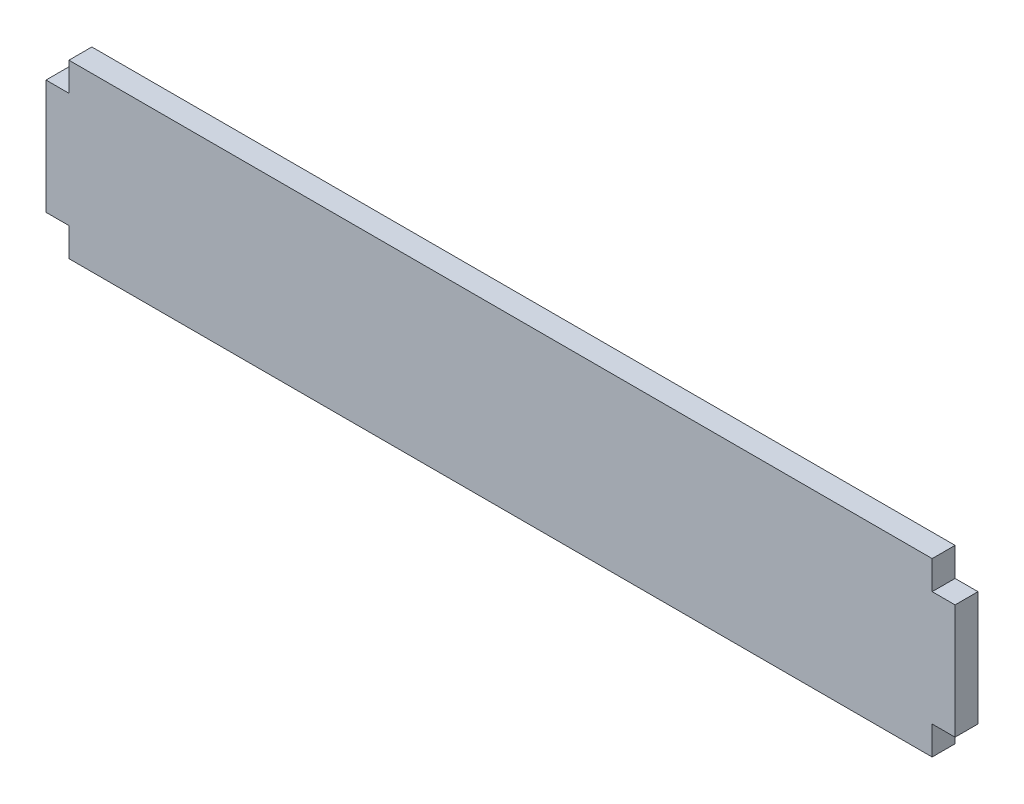
SolidWorks part; units mm, degrees
ref_plane "Alzado" through (0, 0, 0) normal (0, 0, 1) x (1, 0, 0)
ref_plane "Planta" through (0, 0, 0) normal (0, 1, 0) x (1, 0, 0)
ref_plane "Vista lateral" through (0, 0, 0) normal (1, 0, 0) x (0, 0, -1)
sketch "Croquis1" plane through (0, 0, 0) normal (0, 0, 1) x (1, 0, 0)
  line L1 (-113, -22.5) -> (113, -22.5)
  line L2 (-113, -22.5) -> (-113, 22.5)
  line L3 (-113, 22.5) -> (113, 22.5)
  line L4 (113, -22.5) -> (113, 22.5)
  line L5 (-113, -22.5) -> (113, 22.5) construction
  line L6 (-113, 22.5) -> (113, -22.5) construction
  point P0 (0, 0)
  dimension "D1" = 226
  dimension "D2" = 45
extrude "Saliente-Extruir1" add sketch "Croquis1" along normal blind 6
sketch "Croquis2" plane through (-113, 0, 0) normal (-1, 0, 0) x (0, 0, 1)
  line L0 (6, 22.5) -> (6, -22.5) construction
  line L1 (6, 15) -> (0, 15)
  line L2 (6, 15) -> (6, -15)
  line L3 (6, -15) -> (0, -15)
  line L4 (0, 15) -> (0, -15)
  line L5 (0, 22.5) -> (0, -22.5) construction
  point P8 (6, 0)
  dimension "D1" = 30
extrude "Saliente-Extruir2" add sketch "Croquis2" along normal blind 6 and the other way blind 232
